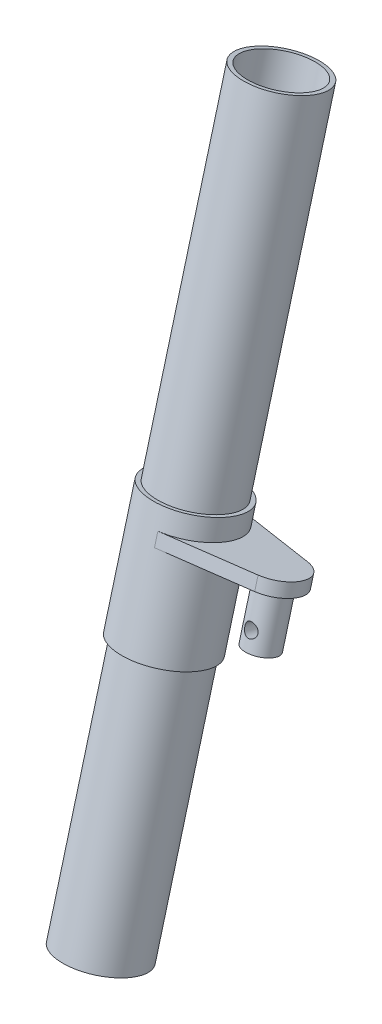
SolidWorks part; units mm, degrees
material "AISI 316 Stainless Steel Sheet (SS)"
ref_plane "Front Plane" through (0, 0, 0) normal (0, 0, 1) x (1, 0, 0)
ref_plane "Top Plane" through (0, 0, 0) normal (0, 1, 0) x (1, 0, 0)
ref_plane "Right Plane" through (0, 0, 0) normal (1, 0, 0) x (0, 0, -1)
sketch "Sketch2" plane through (0, 0, 0) normal (1, 0, 0) x (0, 0, -1)
  line L0 (0, 0) -> (-50000, 0) construction
  line L1 (0, 0) -> (0, 50000) construction
  line L2 (15.5291, 57.9555) -> (-10.3528, -38.637) construction
  line L3 (37.0307, 80.2449) -> (-66.4969, -306.1254)
  line L4 (-66.4969, -306.1254) -> (-88.2302, -300.302)
  line L5 (37.0307, 80.2449) -> (15.2974, 86.0684)
  line L6 (-88.2302, -300.302) -> (15.2974, 86.0684)
  dimension "D1" = 15
  dimension "D2" = 60
  dimension "D3" = 40
  dimension "D4" = 400
  dimension "D5" = 15
  dimension "D6" = 22.5
revolve "Revolve1" add sketch "Sketch2" angle 360 about L6
sketch "Sketch3" plane through (0, 0, 0) normal (1, 0, 0) x (0, 0, -1)
  line L0 (-88.2302, -300.302) -> (15.2974, 86.0684) construction
  line L2 (-12.1449, -103.281) -> (-30.2622, -170.8958)
  line L3 (-12.1449, -103.281) -> (-9.7301, -103.928)
  line L4 (-9.7301, -103.928) -> (-27.8474, -171.5428)
  line L5 (-27.8474, -171.5428) -> (-30.2622, -170.8958)
  line L6 (-66.4969, -306.1254) -> (-88.2302, -300.302) construction
  line L7 (0, 0) -> (-30.5534, -114.027) construction
  line L8 (0, -200000) -> (0, 250000) construction
  dimension "D1" = 22.5
  dimension "D2" = 2.5
  dimension "D3" = 70
  dimension "D4" = 140
  dimension "D5" = 15
  dimension "D6" = 195
revolve "Revolve2" add sketch "Sketch3" angle 360 about L6
ref_plane "Plane1" through (0, -114.027, 30.5534) normal (0, 0.9659, -0.2588) x (1, 0, 0)
sketch "Sketch4" plane through (0, -114.027, 30.5534) normal (0, 0.9659, -0.2588) x (1, 0, 0)
  line L0 (0, 0) -> (0, 50000) construction
  line L1 (0, -7.5) -> (50000, -7.5) construction
  line L2 (53, 7.1969) -> (5, 16.9949)
  line L3 (53, -22.1969) -> (5, -31.9949)
  circle A0 centre (0, -7.5) radius 25 construction
  arc A1 (5, -31.9949) -> (5, 16.9949) centre (0, -7.5) ccw
  arc A2 (53, -22.1969) -> (53, 7.1969) centre (50, -7.5) ccw
  dimension "D1" = 30
  dimension "D2" = 50
extrude "Boss-Extrude1" add sketch "Sketch4" along normal mid plane 7.5 separate body
sketch "Sketch5" plane through (0, -117.6492, 31.524) normal (0, -0.9659, 0.2588) x (1, 0, 0)
  circle A0 centre (50, 7.5) radius 9
  point P5 (50, 7.5)
  dimension "D1" = 18
extrude "Boss-Extrude2" add sketch "Sketch5" along normal blind 30
ref_plane "Plane2" through (0, 1.9411, 7.2444) normal (0, 0.2588, 0.9659) x (1, 0, 0)
sketch "Sketch6" plane through (0, 1.9411, 7.2444) normal (0, 0.2588, 0.9659) x (1, 0, 0)
  line L0 (50, -151.7994) -> (50, -121.7994) construction
  line L1 (41, -151.7994) -> (59, -151.7994) construction
  circle A0 centre (50, -141.7994) radius 3.75
  dimension "D2" = 7.5
  dimension "D1" = 10
shell "Shell1" thickness 2.5
extrude "Cut-Extrude2" cut sketch "Sketch6" against normal through all both and the other way through all
